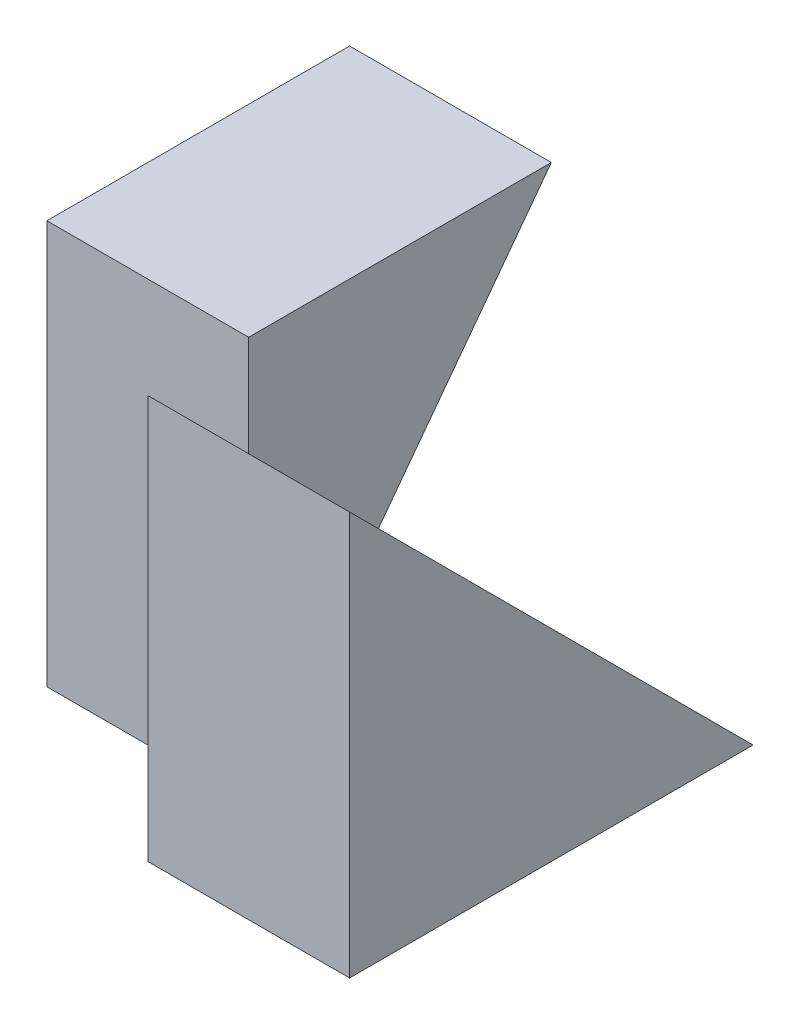
SolidWorks part; units mm, degrees
ref_plane "Front Plane" through (0, 0, 0) normal (0, 0, 1) x (1, 0, 0)
ref_plane "Top Plane" through (0, 0, 0) normal (0, 1, 0) x (1, 0, 0)
ref_plane "Right Plane" through (0, 0, 0) normal (1, 0, 0) x (0, 0, -1)
sketch "Sketch1" plane through (0, 0, 0) normal (1, 0, 0) x (0, 0, -1)
  line L1 (0, 0) -> (4, 0)
  line L2 (0, 0) -> (0, 4)
  line L3 (0, 4) -> (4, 4)
  line L4 (4, 0) -> (4, 4)
  dimension "D1" = 4
  dimension "D2" = 4
extrude "Boss-Extrude1" add sketch "Sketch1" along normal blind 2
sketch "Sketch2" plane through (0, 0, 0) normal (-1, 0, 0) x (0, 0, 1)
  line L0 (-1, 0) -> (-1, 4)
  line L1 (0, 0) -> (-4, 0) construction
  line L2 (-4, 0) -> (-4, 4) construction
  line L3 (-4, 4) -> (-4, 0)
  line L4 (-4, 0) -> (-1, 0)
  line L5 (-4, 4) -> (0, 4) construction
  line L6 (-1, 4) -> (-4, 4)
  dimension "D1" = 3
  dimension "D2" = 4
extrude "Boss-Extrude2" add sketch "Sketch2" along normal blind 2
sketch "Sketch3" plane through (2, 0, 0) normal (1, 0, 0) x (0, 0, -1)
  line L0 (4, 0) -> (0, 4)
  line L1 (0, 4) -> (0, 0) construction
  line L2 (0, 4) -> (4, 4)
  line L3 (4, 4) -> (4, 0)
extrude "Cut-Extrude1" cut sketch "Sketch3" against normal blind 2
sketch "Sketch4" plane through (-2, 0, 0) normal (-1, 0, 0) x (0, 0, 1)
  line L0 (-1, 0) -> (-4, 4)
  line L1 (-4, 4) -> (-1, 4)
  line L2 (-1, 4) -> (-1, 0)
  line M4 (-4, 0) -> (-1, 0)
  line M7 (-4, 4) -> (-4, 0)
extrude "Cut-Extrude2" cut sketch "Sketch4" against normal blind 2 contours L0 M4 M7
